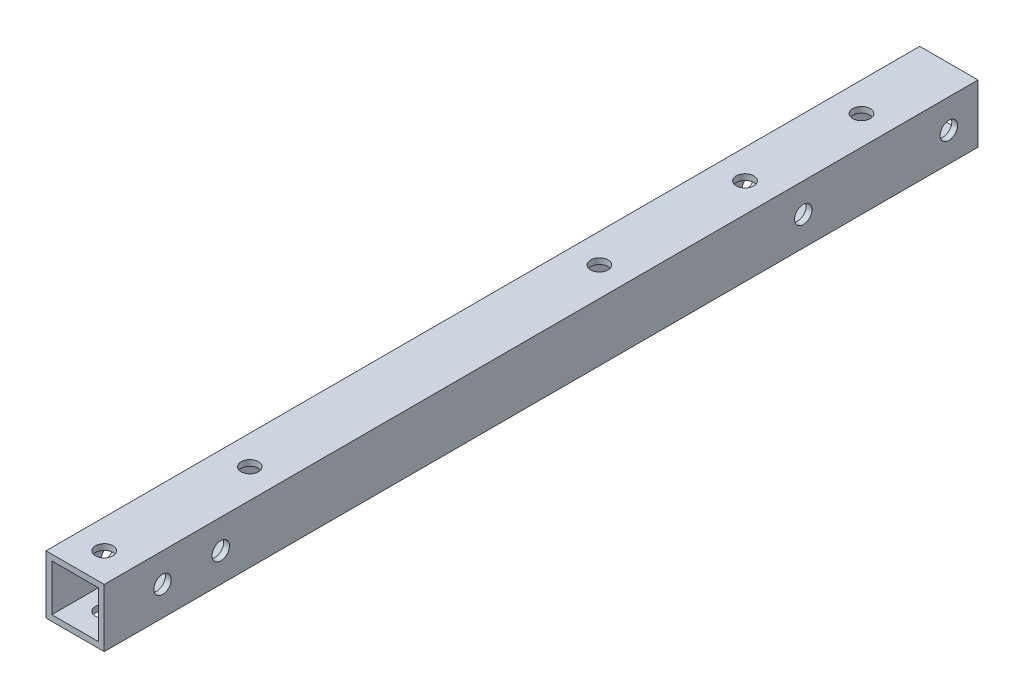
SolidWorks part; units mm, degrees
material "6063-O"
ref_plane "前视基准面" through (0, 0, 0) normal (0, 0, 1) x (1, 0, 0)
ref_plane "上视基准面" through (0, 0, 0) normal (0, 1, 0) x (1, 0, 0)
ref_plane "右视基准面" through (0, 0, 0) normal (1, 0, 0) x (0, 0, -1)
other "Configuration Table"
sketch "草图1" plane through (0, 0, 0) normal (0, 0, 1) x (1, 0, 0)
  line L1 (216.7038, 104.4873) -> (206.7038, 104.4873)
  line L2 (216.7038, 104.4873) -> (216.7038, 94.4873)
  line L3 (216.7038, 94.4873) -> (206.7038, 94.4873)
  line L4 (206.7038, 104.4873) -> (206.7038, 94.4873)
  line L5 (216.7038, 104.4873) -> (206.7038, 94.4873) construction
  line L6 (216.7038, 94.4873) -> (206.7038, 104.4873) construction
  point P4 (211.7038, 99.4873)
  dimension "D1" = 10
  dimension "D2" = 10
extrude "拉伸-薄壁1" add sketch "草图1" along normal blind 150 thin thin type one direction reverse wall 1
sketch "草图2" plane through (216.7038, 0, 0) normal (1, 0, 0) x (0, 0, -1)
  line L0 (-150, 99.4873) -> (0, 99.4873) construction
  line L1 (-150, 94.4873) -> (-150, 104.4873) construction
  line L2 (0, 94.4873) -> (0, 104.4873) construction
  circle A0 centre (-30, 99.4873) radius 1.5
  circle A1 centre (-5, 99.4873) radius 1.5
  circle A2 centre (-60, 99.4873) radius 1.5 construction
  circle A3 centre (-130, 99.4873) radius 1.5
  circle A4 centre (-140, 99.4873) radius 1.5
  dimension "D1" = 3
  dimension "D2" = 25
  dimension "D3" = 30
  dimension "D4" = 5
  dimension "D6" = 10
  dimension "D5" = 10
extrude "切除-拉伸1" cut sketch "草图2" against normal through all
sketch "草图3" plane through (0, 94.4873, 0) normal (0, -1, 0) x (1, 0, 0)
  line L0 (211.7038, 0) -> (211.7038, 150) construction
  line L1 (206.7038, 0) -> (216.7038, 0) construction
  line L2 (206.7038, 150) -> (216.7038, 150) construction
  line L6 (216.7038, 0) -> (206.7038, 0) construction
  circle A2 centre (211.7038, 120) radius 1.5
  circle A4 centre (211.7038, 35) radius 1.5
  circle A5 centre (211.7038, 145) radius 1.5
  circle A6 centre (211.7038, 60) radius 1.5
  circle A7 centre (211.7038, 15) radius 1.5
  dimension "D3" = 20
  dimension "D4" = 15
  dimension "D5" = 25
  dimension "D6" = 25
  dimension "D7" = 110
  dimension "D1" = 3
extrude "切除-拉伸2" cut sketch "草图3" against normal through all
